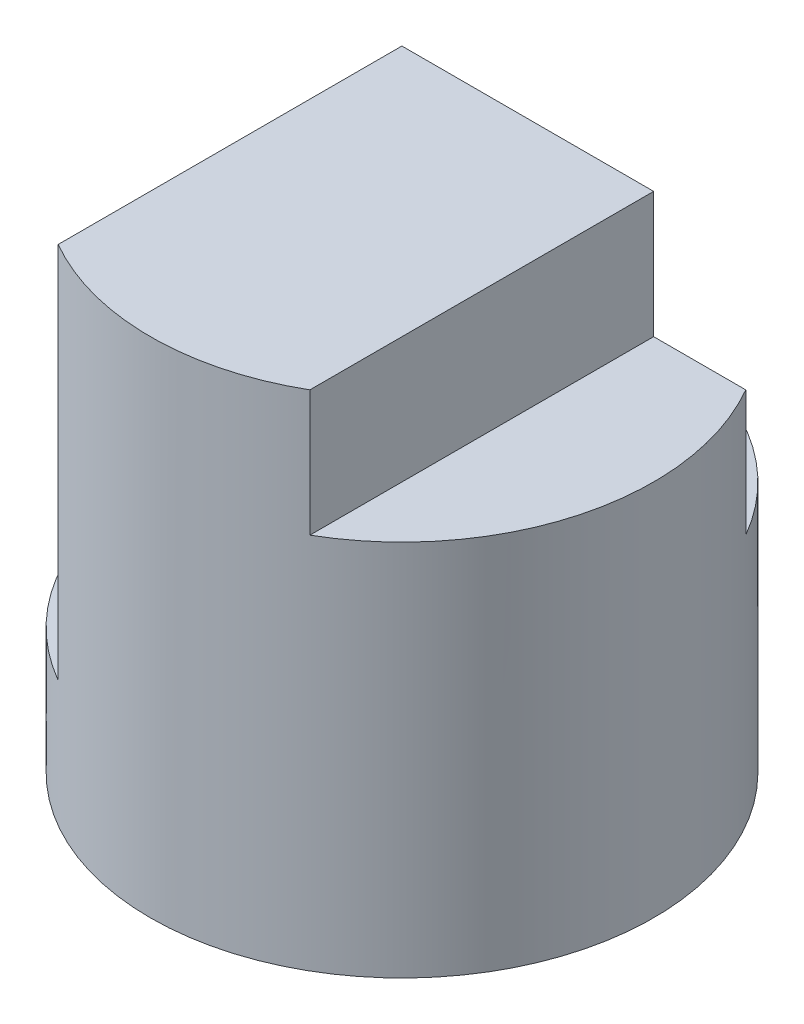
SolidWorks part; units mm, degrees
ref_plane "Front" through (0, 0, 0) normal (0, 0, 1) x (1, 0, 0)
ref_plane "Top" through (0, 0, 0) normal (0, 1, 0) x (1, 0, 0)
ref_plane "Right" through (0, 0, 0) normal (1, 0, 0) x (0, 0, -1)
sketch "Sketch1" plane through (0, 0, 0) normal (0, 1, 0) x (1, 0, 0)
  circle A0 centre (0, 0) radius 2
  dimension "D1" = 4
extrude "Boss-Extrude1" add sketch "Sketch1" along normal blind 4
sketch "Sketch2" plane through (0, 0, 0) normal (0, 0, 1) x (1, 0, 0)
  line L0 (1, 4) -> (-2, 4)
  line L18 (-2, 4) -> (-2, 2)
  line L19 (-2, 4) -> (-2, 0) construction
  line L20 (-2, 2) -> (-1.0009, 2)
  line L21 (-1.0009, 2) -> (-1.0009, 3)
  line L24 (-1.0009, 3) -> (-1.0009, 4)
  line L25 (-1.0009, 4) -> (-2, 4)
  line L27 (2, 4) -> (1, 4)
  line L28 (2, 4) -> (2, 3)
  line L29 (2, 3) -> (1, 3)
  line L30 (1, 4) -> (1, 3)
  dimension "D2" = 0.9991
extrude "Cut-Extrude1" cut sketch "Sketch2" against normal mid plane 4 contours L21 L24 L0 L18 L20 | L27 L30 L29 L28
sketch "Sketch3" plane through (0, 4, 0) normal (0, 1, 0) x (1, 0, 0)
  line L0 (-1.7321, 1) -> (1.7321, 1)
  arc A0 (-1.0009, 1.7315) -> (-1.0009, -1.7315) centre (0, 0) ccw construction
  arc A2 (-1.7321, 1) -> (1.7321, 1) centre (0, 0) cw
  point P6 (0, 0)
  dimension "D1" = 1
extrude "Cut-Extrude2" cut sketch "Sketch3" against normal blind 2
sketch "Sketch4" plane through (0, 0, 0) normal (0, 0, 1) x (1, 0, 0)
  line L0 (-2, 2) -> (-2, 0) construction
  line L1 (-1.0009, 2) -> (-2, 2)
  line L2 (-1.0009, 2) -> (-1.0009, 1)
  line L3 (-1.0009, 1) -> (-2, 1)
  line L4 (-2, 2) -> (-2, 1)
extrude "Cut-Extrude3" cut sketch "Sketch4" against normal blind 1 and the other way blind 2
